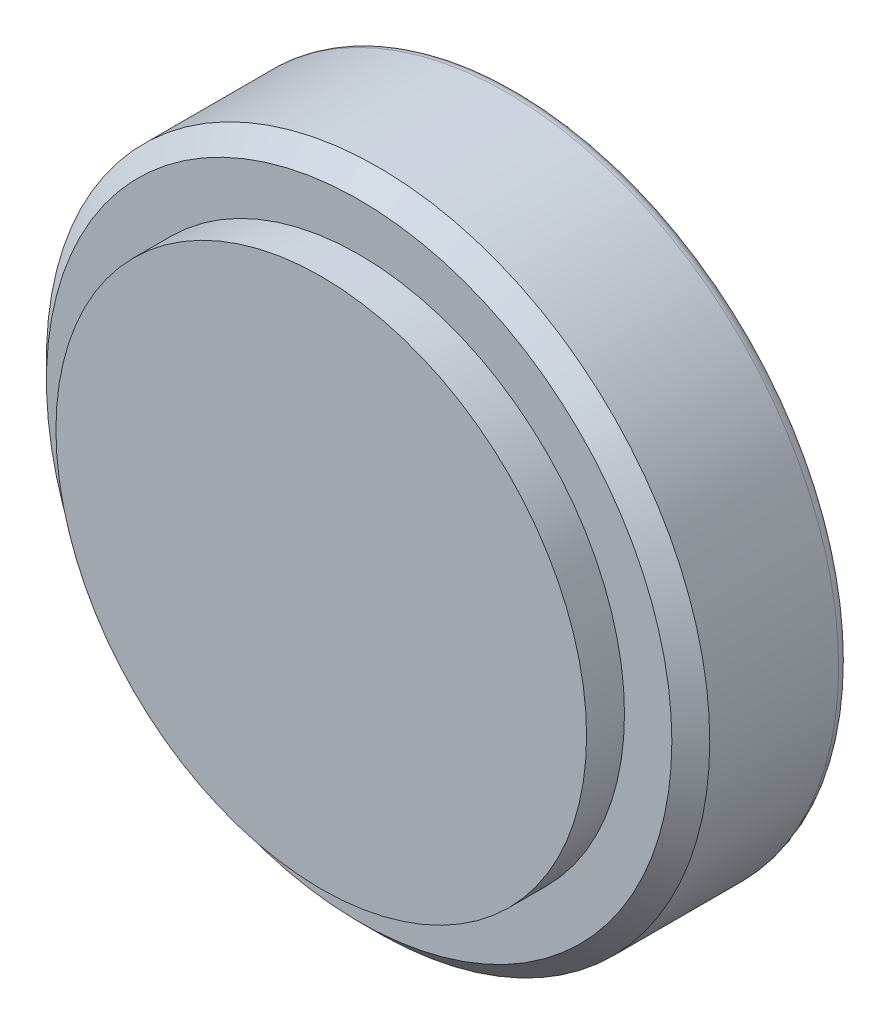
SolidWorks part; units mm, degrees
ref_plane "Front Plane" through (0, 0, 0) normal (0, 0, 1) x (1, 0, 0)
ref_plane "Top Plane" through (0, 0, 0) normal (0, 1, 0) x (1, 0, 0)
ref_plane "Right Plane" through (0, 0, 0) normal (1, 0, 0) x (0, 0, -1)
sketch "Sketch1" plane through (0, 0, 0) normal (0, 0, 1) x (1, 0, 0)
  circle A0 centre (0, 0) radius 87.5
  dimension "D1" = 175
extrude "Boss-Extrude1" add sketch "Sketch1" along normal mid plane 52
sketch "Sketch2" plane through (0, 0, 26) normal (0, 0, 1) x (1, 0, 0)
  circle A0 centre (0, 0) radius 70
  circle A1 centre (0, 0) radius 107.5286
  dimension "D1" = 140
extrude "Cut-Extrude1" cut sketch "Sketch2" against normal blind 10
chamfer "Chamfer1" distance 5 angle 45 1 edges at (87.5, 0, 16)
sketch "Sketch3" plane through (0, 0, -26) normal (0, 0, -1) x (-1, 0, 0)
  line L0 (0, 0) -> (0, 87.5) construction
  line L1 (-20, 75) -> (20, 75)
  line L2 (-20, 75) -> (-20, -75)
  line L3 (-20, -75) -> (20, -75)
  line L4 (20, 75) -> (20, -75)
  line L5 (0, 0) -> (45.4222, 0) construction
  circle A0 centre (0, 0) radius 87.5 construction
  dimension "D1" = 40
  dimension "D2" = 40
  dimension "D3" = 150
  dimension "D4" = 150
extrude "Cut-Extrude2" [suppressed] cut sketch "Sketch3" against normal blind 10
fillet "Fillet1" radius 3 1 edges at (87.5, 0, -26)
